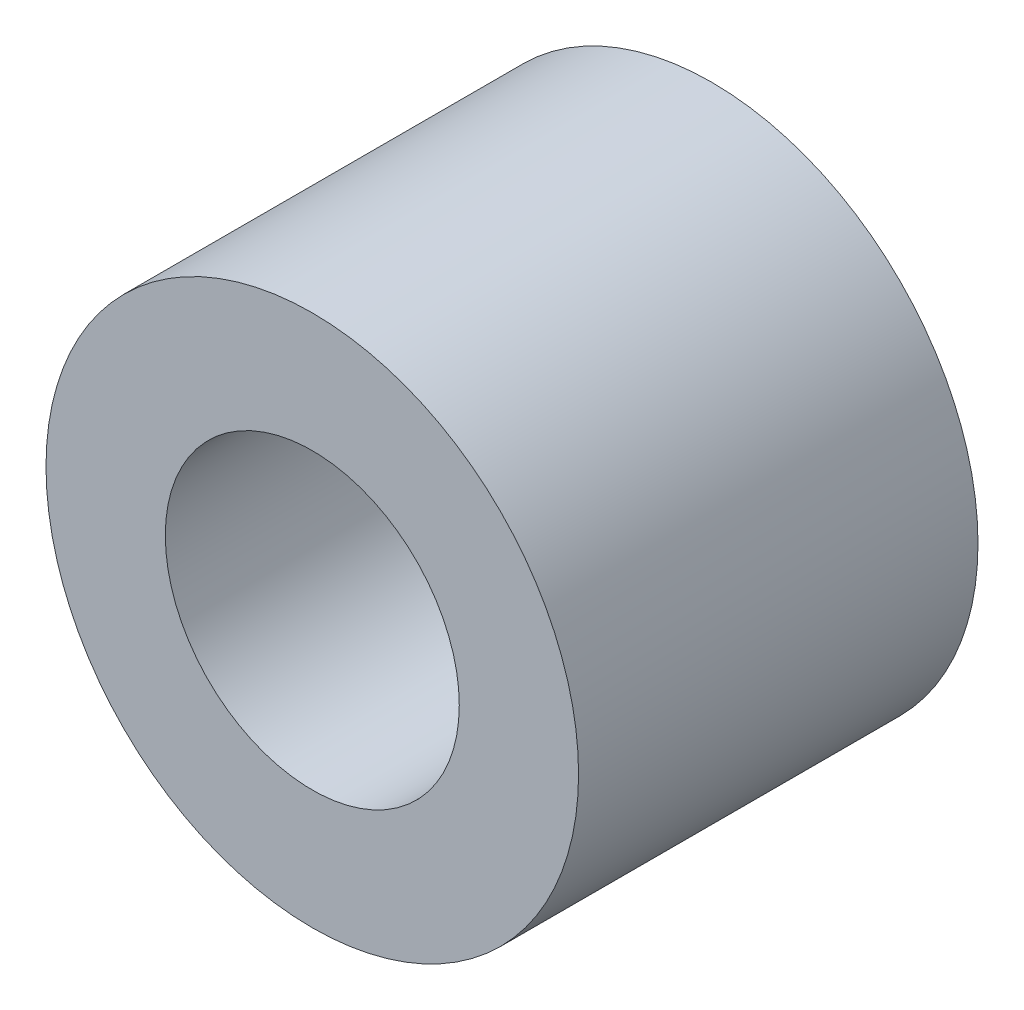
SolidWorks part; units mm, degrees
ref_plane "Front Plane" through (0, 0, 0) normal (0, 0, 1) x (1, 0, 0)
ref_plane "Top Plane" through (0, 0, 0) normal (0, 1, 0) x (1, 0, 0)
ref_plane "Right Plane" through (0, 0, 0) normal (1, 0, 0) x (0, 0, -1)
sketch "Sketch1" plane through (0, 0, 0) normal (0, 0, 1) x (1, 0, 0)
  line L0 (0, 3.175) -> (0, -3.175) construction
  line L1 (0, -3.7719) -> (0, 3.7719) construction
  circle A0 centre (0, 0) radius 1.7526 construction
  circle A1 centre (0, 0) radius 3.175 construction
  point P4 (0, -1.7526)
  point P9 (0, 0)
  point P11 (0, -3.175)
  dimension "ID" = 3.5052
  dimension "OD" = 6.35
sketch "Sketch2" plane through (0, 0, 0) normal (1, 0, 0) x (0, 0, -1)
  line L0 (-2.3813, 0) -> (2.3813, 0) construction
  line L1 (3.7719, 0) -> (-3.7719, 0) construction
  line L2 (-2.3813, -3.175) -> (2.3813, -3.175) construction
  line L4 (0, 3.175) -> (0, -3.175) construction
  point P6 (0, 0)
  point P9 (0, -3.175)
  dimension "Thickness" = 4.7625
sketch "Sketch3" plane through (0, 0, 0) normal (0, 0, 1) x (1, 0, 0)
  circle A0 centre (0, 0) radius 1.7526
  circle A1 centre (0, 0) radius 3.175
  dimension "D1" = 3.5052
  dimension "D2" = 6.35
extrude "Extrude1" add sketch "Sketch3" against normal mid plane 4.7625
equation "\"D1@Sketch3\"=\"ID@Sketch1\""
equation "\"D2@Sketch3\"=\"OD@Sketch1\""
equation "\"Thickness@Extrude1\"=\"Thickness@Sketch2\""
